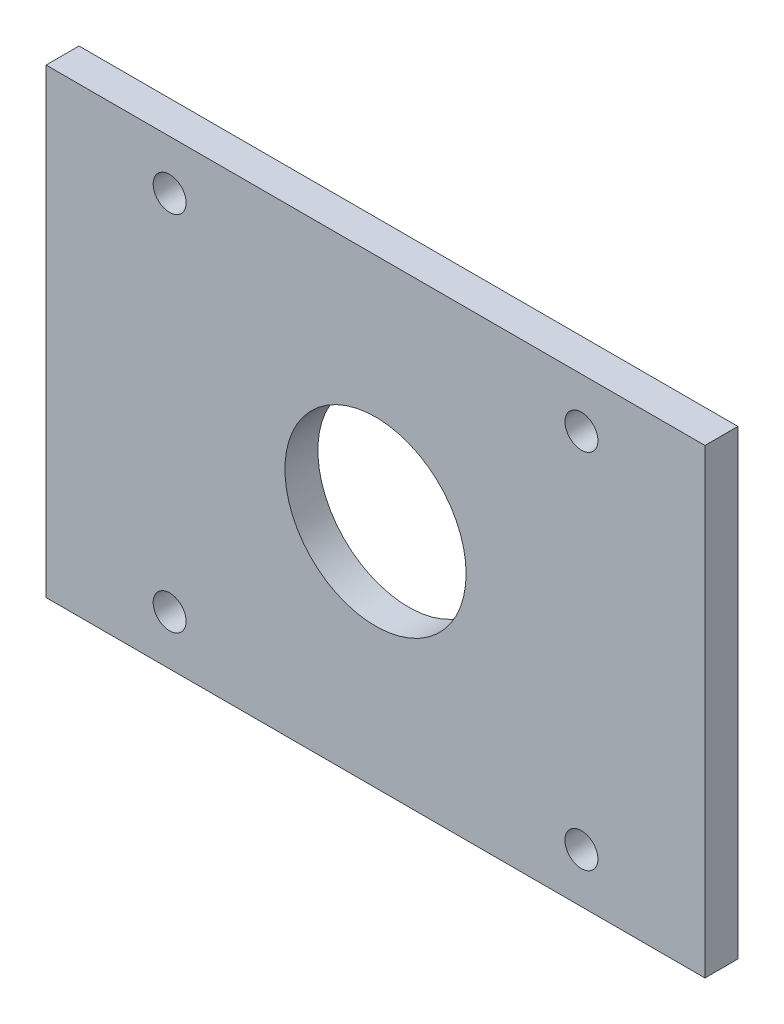
SolidWorks part; units mm, degrees
ref_plane "Front" through (0, 0, 0) normal (0, 0, 1) x (1, 0, 0)
ref_plane "Top" through (0, 0, 0) normal (0, 1, 0) x (1, 0, 0)
ref_plane "Right" through (0, 0, 0) normal (1, 0, 0) x (0, 0, -1)
sketch "草图1" plane through (0, 0, 0) normal (0, 0, 1) x (1, 0, 0)
  line L0 (-40, -35) -> (-40, 35) construction
  line L1 (40, -21) -> (-40, -21)
  line L2 (40, -21) -> (40, 35)
  line L3 (40, 35) -> (-40, 35)
  line L4 (-40, -21) -> (-40, 35)
  line L5 (40, -21) -> (-40, 35) construction
  line L6 (40, 35) -> (-40, -21) construction
  circle A1 centre (0, 7) radius 11
  point P0 (0, 7)
  dimension "D2" = 22
  dimension "D1" = 80
extrude "凸台-拉伸1" add sketch "草图1" along normal blind 4
sketch "草图2" plane through (0, 0, 4) normal (0, 0, 1) x (1, 0, 0)
  line L0 (-40, -35) -> (-40, 35) construction
  line L1 (-40, -21) -> (40, -21) construction
  circle A0 centre (-25, -15) radius 2
  dimension "D1" = 4
  dimension "D2" = 15
  dimension "D3" = 6
extrude "切除-拉伸1" cut sketch "草图2" against normal blind 100
pattern_linear "阵列(线性)1" count 2 spacing 44 along (0, 1, 0) count 2 spacing 50 along (1, 0, 0) of "切除-拉伸1"
